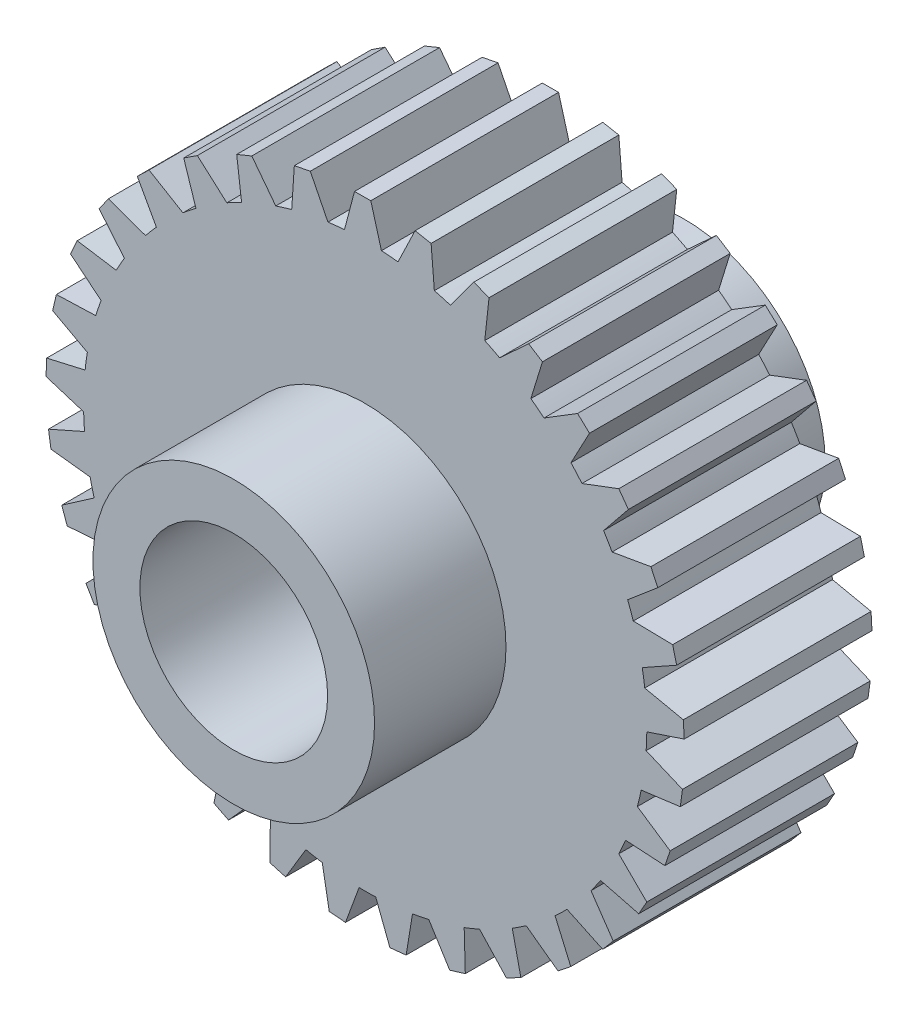
SolidWorks part; units mm, degrees
ref_plane "Front Plane" through (0, 0, 0) normal (0, 0, 1) x (1, 0, 0)
ref_plane "Top Plane" through (0, 0, 0) normal (0, 1, 0) x (1, 0, 0)
ref_plane "Right Plane" through (0, 0, 0) normal (1, 0, 0) x (0, 0, -1)
sketch "Sketch1" plane through (0, 0, 0) normal (0, 0, 1) x (1, 0, 0)
  line L0 (-1.1026, 14.9594) -> (-0.569, 16.9905)
  line L1 (-0.569, 16.9905) -> (0.2995, 16.9974)
  line L2 (0.2995, 16.9974) -> (0.8653, 14.975)
  line L3 (3.5108, 16.6335) -> (3.6837, 14.5406)
  line L4 (1.7484, 14.8978) -> (2.6568, 16.7911)
  line L5 (2.6568, 16.7911) -> (3.5108, 16.6335)
  line L6 (6.5953, 15.6685) -> (6.369, 13.5807)
  line L7 (4.5362, 14.2977) -> (5.7865, 15.9849)
  line L8 (5.7865, 15.9849) -> (6.5953, 15.6685)
  line L9 (9.4414, 14.1372) -> (8.824, 12.13)
  line L10 (7.1601, 13.1808) -> (8.7071, 14.6009)
  line L11 (8.7071, 14.6009) -> (9.4414, 14.1372)
  line L12 (11.9463, 12.0949) -> (10.9602, 10.2408)
  line L13 (9.5252, 11.5875) -> (11.313, 12.6892)
  line L14 (11.313, 12.6892) -> (11.9463, 12.0949)
  line L15 (14.0194, 9.6155) -> (12.7002, 7.9815)
  line L16 (11.546, 9.5755) -> (13.51, 10.3189)
  line L17 (13.51, 10.3189) -> (14.0194, 9.6155)
  line L18 (15.5857, 6.7886) -> (13.9812, 5.4338)
  line L19 (13.1495, 7.2174) -> (15.2187, 7.5757)
  line L20 (15.2187, 7.5757) -> (15.5857, 6.7886)
  line L21 (16.5888, 3.7163) -> (14.7569, 2.6896)
  line L22 (14.2778, 4.5984) -> (16.3774, 4.5586)
  line L23 (16.3774, 4.5586) -> (16.5888, 3.7163)
  line L24 (16.9924, 0.5096) -> (14.9992, -0.1518)
  line L25 (14.89, 1.8132) -> (16.9442, 1.3768)
  line L26 (16.9442, 1.3768) -> (16.9924, 0.5096)
  line L27 (16.7817, -2.7154) -> (14.6995, -2.9876)
  line L28 (14.9641, -1.0375) -> (16.8985, -1.8548)
  line L29 (16.8985, -1.8548) -> (16.7817, -2.7154)
  line L30 (15.9646, -5.8423) -> (13.8684, -5.7155)
  line L31 (14.4973, -3.8508) -> (16.2421, -5.0194)
  line L32 (16.2421, -5.0194) -> (15.9646, -5.8423)
  line L33 (14.5704, -8.758) -> (12.5361, -8.2369)
  line L34 (13.5066, -6.5248) -> (14.9987, -8.0025)
  line L35 (14.9987, -8.0025) -> (14.5704, -8.758)
  line L36 (12.6496, -11.3572) -> (10.7507, -10.4605)
  line L37 (12.0276, -8.963) -> (13.2131, -10.6964)
  line L38 (13.2131, -10.6964) -> (12.6496, -11.3572)
  line L39 (10.2717, -13.5459) -> (8.5768, -12.306)
  line L40 (10.114, -11.0773) -> (10.9501, -13.0037)
  line L41 (10.9501, -13.0037) -> (10.2717, -13.5459)
  line L42 (7.5225, -15.2451) -> (6.0929, -13.7068)
  line L43 (7.8349, -12.7912) -> (8.2912, -14.841)
  line L44 (8.2912, -14.841) -> (7.5225, -15.2451)
  line L45 (4.5014, -16.3932) -> (3.3887, -14.6122)
  line L46 (5.2725, -14.0428) -> (5.3327, -16.1419)
  line L47 (5.3327, -16.1419) -> (4.5014, -16.3932)
  line L48 (1.3176, -16.9489) -> (0.5621, -14.9895)
  line L49 (2.5196, -14.7869) -> (2.1814, -16.8595)
  line L50 (2.1814, -16.8595) -> (1.3176, -16.9489)
  line L51 (-1.9138, -16.8919) -> (-2.2848, -14.825)
  line L52 (-0.3243, -14.9965) -> (-1.0487, -16.9676)
  line L53 (-1.0487, -16.9676) -> (-1.9138, -16.8919)
  line L54 (-5.076, -16.2245) -> (-5.0492, -14.1247)
  line L55 (-3.1566, -14.6641) -> (-4.2408, -16.4625)
  line L56 (-4.2408, -16.4625) -> (-5.076, -16.2245)
  line L57 (-8.0548, -14.9706) -> (-7.631, -12.9138)
  line L58 (-5.8747, -13.8017) -> (-7.2798, -15.3625)
  line L59 (-7.2798, -15.3625) -> (-8.0548, -14.9706)
  line L60 (-10.7425, -13.1757) -> (-9.9371, -11.2363)
  line L61 (-8.3806, -12.4405) -> (-10.0556, -13.7071)
  line L62 (-10.0556, -13.7071) -> (-10.7425, -13.1757)
  line L63 (-13.0419, -10.9046) -> (-11.884, -9.1526)
  line L64 (-10.5835, -10.6297) -> (-12.468, -11.5564)
  line L65 (-12.468, -11.5564) -> (-13.0419, -10.9046)
  line L66 (-14.8699, -8.2393) -> (-13.4014, -6.7382)
  line L67 (-12.4039, -8.4346) -> (-14.4297, -8.988)
  line L68 (-14.4297, -8.988) -> (-14.8699, -8.2393)
  line L69 (-16.1605, -5.2763) -> (-14.4344, -4.0802)
  line L70 (-13.776, -5.9347) -> (-15.8699, -6.0947)
  line L71 (-15.8699, -6.0947) -> (-16.1605, -5.2763)
  line L72 (-16.867, -2.1226) -> (-14.9457, -1.2747)
  line L73 (-14.6502, -3.2204) -> (-16.7366, -2.9812)
  line L74 (-16.7366, -2.9812) -> (-16.867, -2.1226)
  line L75 (-16.9639, 1.1079) -> (-14.9169, 1.5768)
  line L76 (-14.9949, -0.3896) -> (-16.9983, 0.2401)
  line L77 (-16.9983, 0.2401) -> (-16.9639, 1.1079)
  line L78 (-16.4476, 4.2983) -> (-14.3489, 4.3714)
  line L79 (-14.7977, 2.4553) -> (-16.6457, 3.4527)
  line L80 (-16.6457, 3.4527) -> (-16.4476, 4.2983)
  line L81 (-15.3369, 7.3334) -> (-13.2623, 7.0079)
  line L82 (-14.0656, 5.2114) -> (-15.6914, 6.5405)
  line L83 (-15.6914, 6.5405) -> (-15.3369, 7.3334)
  line L84 (-13.6719, 10.1034) -> (-11.6964, 9.3912)
  line L85 (-12.8252, 7.7791) -> (-14.1701, 9.392)
  line L86 (-14.1701, 9.392) -> (-13.6719, 10.1034)
  line L87 (-11.5128, 12.5082) -> (-9.7077, 11.435)
  line L88 (-11.1212, 10.0657) -> (-12.1366, 11.904)
  line L89 (-12.1366, 11.904) -> (-11.5128, 12.5082)
  line L90 (-8.9375, 14.461) -> (-7.3682, 13.0656)
  line L91 (-9.0153, 11.9885) -> (-9.6644, 13.9857)
  line L92 (-9.6644, 13.9857) -> (-8.9375, 14.461)
  line L93 (-6.0393, 15.8911) -> (-4.7624, 14.2239)
  line L94 (-6.5835, 13.478) -> (-6.8429, 15.5619)
  line L95 (-6.8429, 15.5619) -> (-6.0393, 15.8911)
  line L96 (-2.9227, 16.7469) -> (-1.9844, 14.8682)
  line L97 (-3.9138, 14.4804) -> (-3.7742, 16.5758)
  line L98 (-3.7742, 16.5758) -> (-2.9227, 16.7469)
  arc A0 (1.7484, 14.8978) -> (0.8653, 14.975) centre (0, 0) ccw
  arc A1 (0.2995, 16.9974) -> (-0.569, 16.9905) centre (0, 0) ccw
  arc A2 (4.5362, 14.2977) -> (3.6837, 14.5406) centre (0, 0) ccw
  circle A3 centre (0, 0) radius 17 construction
  circle A4 centre (0, 0) radius 15 construction
  arc A5 (7.1601, 13.1808) -> (6.369, 13.5807) centre (0, 0) ccw
  arc A6 (9.5252, 11.5875) -> (8.824, 12.13) centre (0, 0) ccw
  arc A7 (11.546, 9.5755) -> (10.9602, 10.2408) centre (0, 0) ccw
  arc A8 (13.1495, 7.2174) -> (12.7002, 7.9815) centre (0, 0) ccw
  arc A9 (14.2778, 4.5984) -> (13.9812, 5.4338) centre (0, 0) ccw
  arc A10 (14.89, 1.8132) -> (14.7569, 2.6896) centre (0, 0) ccw
  arc A11 (14.9641, -1.0375) -> (14.9992, -0.1518) centre (0, 0) ccw
  arc A12 (14.4973, -3.8508) -> (14.6995, -2.9876) centre (0, 0) ccw
  arc A13 (13.5066, -6.5248) -> (13.8684, -5.7155) centre (0, 0) ccw
  arc A14 (12.0276, -8.963) -> (12.5361, -8.2369) centre (0, 0) ccw
  arc A15 (10.114, -11.0773) -> (10.7507, -10.4605) centre (0, 0) ccw
  arc A16 (7.8349, -12.7912) -> (8.5768, -12.306) centre (0, 0) ccw
  arc A17 (5.2725, -14.0428) -> (6.0929, -13.7068) centre (0, 0) ccw
  arc A18 (2.5196, -14.7869) -> (3.3887, -14.6122) centre (0, 0) ccw
  arc A19 (-0.3243, -14.9965) -> (0.5621, -14.9895) centre (0, 0) ccw
  arc A20 (-3.1566, -14.6641) -> (-2.2848, -14.825) centre (0, 0) ccw
  arc A21 (-5.8747, -13.8017) -> (-5.0492, -14.1247) centre (0, 0) ccw
  arc A22 (-8.3806, -12.4405) -> (-7.631, -12.9138) centre (0, 0) ccw
  arc A23 (-10.5835, -10.6297) -> (-9.9371, -11.2363) centre (0, 0) ccw
  arc A24 (-12.4039, -8.4346) -> (-11.884, -9.1526) centre (0, 0) ccw
  arc A25 (-13.776, -5.9347) -> (-13.4014, -6.7382) centre (0, 0) ccw
  arc A26 (-14.6502, -3.2204) -> (-14.4344, -4.0802) centre (0, 0) ccw
  arc A27 (-14.9949, -0.3896) -> (-14.9457, -1.2747) centre (0, 0) ccw
  arc A28 (-14.7977, 2.4553) -> (-14.9169, 1.5768) centre (0, 0) ccw
  arc A29 (-1.1026, 14.9594) -> (-1.9844, 14.8682) centre (0, 0) ccw
  arc A30 (-3.9138, 14.4804) -> (-4.7624, 14.2239) centre (0, 0) ccw
  arc A31 (-6.5835, 13.478) -> (-7.3682, 13.0656) centre (0, 0) ccw
  arc A32 (-9.0153, 11.9885) -> (-9.7077, 11.435) centre (0, 0) ccw
  arc A33 (-11.1212, 10.0657) -> (-11.6964, 9.3912) centre (0, 0) ccw
  arc A34 (-12.8252, 7.7791) -> (-13.2623, 7.0079) centre (0, 0) ccw
  arc A35 (-14.0656, 5.2114) -> (-14.3489, 4.3714) centre (0, 0) ccw
  point P7 (17, 0)
  point P11 (14.3446, 4.3856)
  point P140 (0, 0)
  dimension "D1" = 30
  dimension "D3" = 2.1
  dimension "D2" = 2
  dimension "D4" = 33
extrude "Boss-Extrude1" add sketch "Sketch1" along normal mid plane 10 contours L82 A35 L78 L80 L79 A28 L75 L77 L76 A27 L72 L74 L73 A26 L69 L71 L70 A25 L66 L68 L67 A24 L63 L65 L64 A23 L60 L62 L61 A22 L57 L59 L58 A21 L54 L56 L55 A20 L51 L53 L52 A19 L48 L50 L49 A18 L45 L47 L46 A17 L42
sketch "Sketch2" plane through (0, 0, 5) normal (0, 0, 1) x (1, 0, 0)
  circle A0 centre (0, 0) radius 7.5
  dimension "D1" = 15
extrude "Boss-Extrude2" add sketch "Sketch2" along normal blind 7
mirror "Mirror1" about plane through (0, 0, 0) normal (0, 0, 1) of "Boss-Extrude2"
sketch "Sketch3" plane through (0, 0, 12) normal (0, 0, 1) x (1, 0, 0)
  circle A0 centre (0, 0) radius 5
  dimension "D1" = 10
extrude "Cut-Extrude1" cut sketch "Sketch3" against normal through all both and the other way through all
